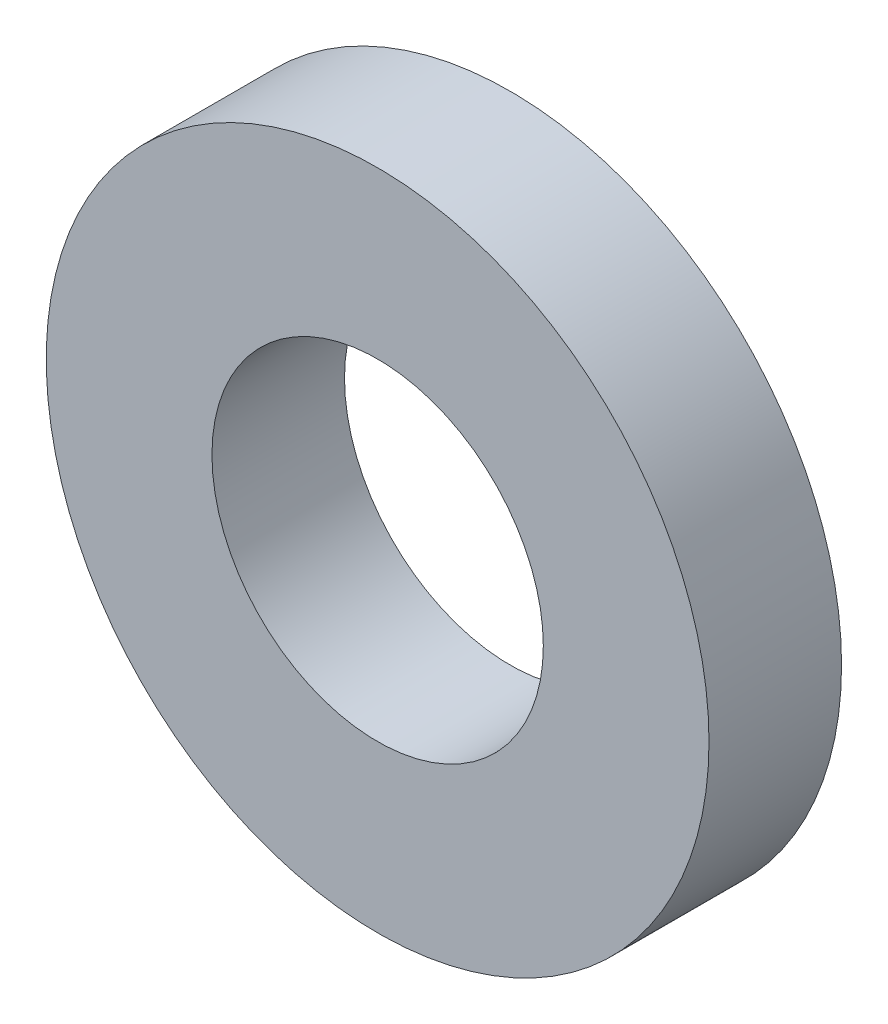
SolidWorks part; units mm, degrees
ref_plane "Front Plane" through (0, 0, 0) normal (0, 0, 1) x (1, 0, 0)
ref_plane "Top Plane" through (0, 0, 0) normal (0, 1, 0) x (1, 0, 0)
ref_plane "Right Plane" through (0, 0, 0) normal (1, 0, 0) x (0, 0, -1)
sketch "Sketch1" plane through (0, 0, 0) normal (0, 0, 1) x (1, 0, 0)
  circle A0 centre (0, 0) radius 10
extrude "Boss-Extrude1" add sketch "Sketch1" along normal blind 4
sketch "Sketch2" plane through (0, 0, 4) normal (0, 0, 1) x (1, 0, 0)
  circle A0 centre (0, 0) radius 5
extrude "Cut-Extrude1" cut sketch "Sketch2" against normal blind 4
